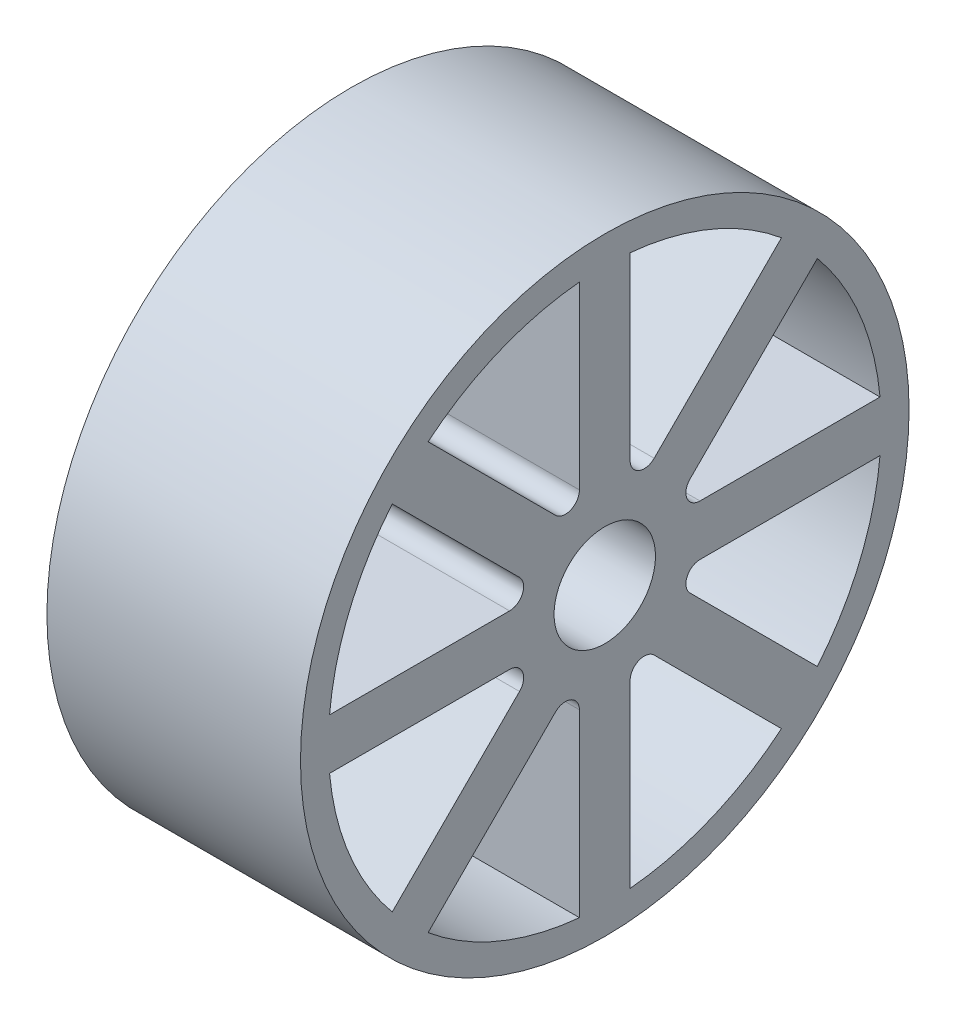
SolidWorks part; units mm, degrees
ref_plane "Front Plane" through (0, 0, 0) normal (0, 0, 1) x (1, 0, 0)
ref_plane "Top Plane" through (0, 0, 0) normal (0, 1, 0) x (1, 0, 0)
ref_plane "Right Plane" through (0, 0, 0) normal (1, 0, 0) x (0, 0, -1)
sketch "Sketch1" plane through (0, 0, 0) normal (1, 0, 0) x (0, 0, -1)
  circle A0 centre (0, 0) radius 27.5
  circle A1 centre (0, 0) radius 5
  dimension "D1" = 10
  dimension "D2" = 55
extrude "Boss-Extrude1" add sketch "Sketch1" along normal blind 25
sketch "Sketch2" plane through (25, 0, 0) normal (1, 0, 0) x (0, 0, -1)
  line L0 (0, 0) -> (0, 27.5) construction
  line L1 (0, 0) -> (19.4454, 19.4454) construction
  line L2 (0, 0) -> (27.5, 0) construction
  line L3 (0, 0) -> (19.4454, -19.4454) construction
  line L4 (0, 0) -> (0, -27.5) construction
  line L5 (0, 0) -> (-19.4454, -19.4454) construction
  line L6 (0, 0) -> (-27.5, 0) construction
  line L7 (0, 0) -> (-19.4454, 19.4454) construction
  line L8 (-2.5, 27.3861) -> (-2.5, 9.3861)
  line L9 (-17.5971, 21.1327) -> (-4.8692, 8.4048)
  line L10 (17.5971, 21.1327) -> (4.8692, 8.4048)
  line L11 (2.5, 27.3861) -> (2.5, 9.3861)
  line L12 (27.3861, 2.5) -> (9.3861, 2.5)
  line L13 (21.1327, 17.5971) -> (8.4048, 4.8692)
  line L14 (21.1327, -17.5971) -> (8.4048, -4.8692)
  line L15 (27.3861, -2.5) -> (9.3861, -2.5)
  line L16 (2.5, -27.3861) -> (2.5, -9.3861)
  line L17 (17.5971, -21.1327) -> (4.8692, -8.4048)
  line L18 (-17.5971, -21.1327) -> (-4.8692, -8.4048)
  line L19 (-2.5, -27.3861) -> (-2.5, -9.3861)
  line L20 (-27.3861, -2.5) -> (-9.3861, -2.5)
  line L21 (-21.1327, -17.5971) -> (-8.4048, -4.8692)
  line L22 (-21.1327, 17.5971) -> (-8.4048, 4.8692)
  line L23 (-27.3861, 2.5) -> (-9.3861, 2.5)
  circle A0 centre (0, 0) radius 27.5 construction
  arc A1 (-4.8692, 8.4048) -> (-2.5, 9.3861) centre (-3.8879, 9.3861) ccw
  arc A2 (-17.5971, 21.1327) -> (-2.5, 27.3861) centre (-2.5, 6.0355) cw
  arc A3 (2.5, 27.3861) -> (17.5971, 21.1327) centre (2.5, 6.0355) cw
  arc A4 (2.5, 9.3861) -> (4.8692, 8.4048) centre (3.8879, 9.3861) ccw
  arc A5 (21.1327, 17.5971) -> (27.3861, 2.5) centre (6.0355, 2.5) cw
  arc A6 (8.4048, 4.8692) -> (9.3861, 2.5) centre (9.3861, 3.8879) ccw
  arc A7 (27.3861, -2.5) -> (21.1327, -17.5971) centre (6.0355, -2.5) cw
  arc A8 (9.3861, -2.5) -> (8.4048, -4.8692) centre (9.3861, -3.8879) ccw
  arc A9 (17.5971, -21.1327) -> (2.5, -27.3861) centre (2.5, -6.0355) cw
  arc A10 (4.8692, -8.4048) -> (2.5, -9.3861) centre (3.8879, -9.3861) ccw
  arc A11 (-2.5, -27.3861) -> (-17.5971, -21.1327) centre (-2.5, -6.0355) cw
  arc A12 (-2.5, -9.3861) -> (-4.8692, -8.4048) centre (-3.8879, -9.3861) ccw
  arc A13 (-21.1327, -17.5971) -> (-27.3861, -2.5) centre (-6.0355, -2.5) cw
  arc A14 (-8.4048, -4.8692) -> (-9.3861, -2.5) centre (-9.3861, -3.8879) ccw
  arc A15 (-27.3861, 2.5) -> (-21.1327, 17.5971) centre (-6.0355, 2.5) cw
  arc A16 (-9.3861, 2.5) -> (-8.4048, 4.8692) centre (-9.3861, 3.8879) ccw
  point P16 (0, 0)
  point P65 (0, 0)
  dimension "D2" = 2.5
  dimension "D3" = 18
  dimension "D4" = 2.5
  dimension "D5" = 8
  dimension "D1" = 8
extrude "Cut-Extrude1" cut sketch "Sketch2" against normal blind 25
sketch "Sketch3" plane through (25, 0, 0) normal (1, 0, 0) x (0, 0, -1)
  circle A0 centre (0, 0) radius 27.25
  circle A1 centre (0, 0) radius 30
  dimension "D1" = 54.5
  dimension "D2" = 60
extrude "Boss-Extrude2" add sketch "Sketch3" against normal blind 25
